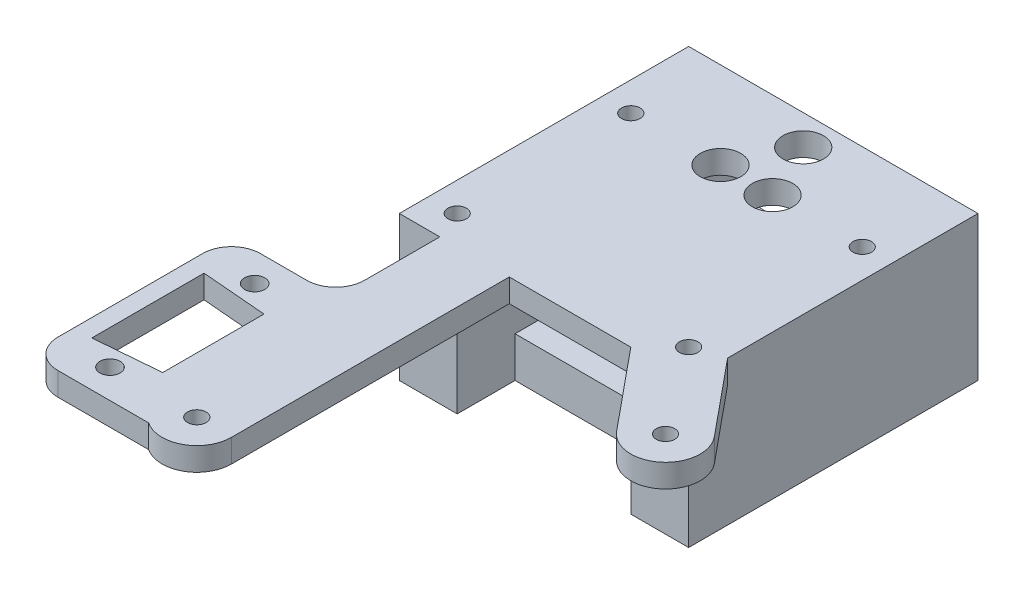
SolidWorks part; units mm, degrees
ref_plane "Plano frontal" through (0, 0, 0) normal (0, 0, 1) x (1, 0, 0)
ref_plane "Plano superior" through (0, 0, 0) normal (0, 1, 0) x (1, 0, 0)
ref_plane "Plano direito" through (0, 0, 0) normal (1, 0, 0) x (0, 0, -1)
sketch "Esboço1" plane through (0, 0, 0) normal (0, 0, 1) x (1, 0, 0)
  line L0 (-25, 0) -> (-15, 0)
  line L1 (-15, 0) -> (-15, -14)
  line L2 (-15, -14) -> (15, -14)
  line L3 (0, 3.4978) -> (0, -21) construction
  line L4 (25, -21) -> (-25, -21)
  line L5 (-25, -21) -> (-25, 0)
  line L6 (25, -21) -> (25, 0)
  line L7 (15, 0) -> (15, -14)
  line L8 (25, 0) -> (15, 0)
  point P9 (-20, 0)
  point P14 (0, -14)
  dimension "D1" = 40
  dimension "D2" = 10
  dimension "D3" = 14
  dimension "D4" = 7
extrude "Ressalto-extrusão1" add sketch "Esboço1" along normal blind 50
sketch "Esboço2" plane through (0, -21, 0) normal (0, -1, 0) x (1, 0, 0)
  line L0 (0, 0) -> (0, 50) construction
  line L1 (-25, 50) -> (25, 50) construction
  line L2 (-25, 0) -> (25, 0) construction
  line L3 (20, 45) -> (-20, 45) construction
  line L4 (20, 45) -> (20, 15) construction
  line L5 (20, 15) -> (-20, 15) construction
  line L6 (-20, 45) -> (-20, 15) construction
  line L7 (20, 45) -> (-20, 15) construction
  line L8 (20, 15) -> (-20, 45) construction
  line L9 (0, 16.6407) -> (0, 2.1283) construction
  circle A0 centre (-20, 45) radius 1.6
  circle A1 centre (20, 45) radius 1.6
  circle A2 centre (20, 15) radius 1.6
  circle A3 centre (-20, 15) radius 1.6
  circle A4 centre (-4.5, 15) radius 1.6
  circle A5 centre (0, 5.2) radius 1.6
  circle A6 centre (4.5, 15) radius 1.6
  point P5 (0, 30)
  dimension "D3" = 3.2
  dimension "D1" = 30
  dimension "D2" = 40
  dimension "D4" = 9
  dimension "D5" = 9.8
  dimension "D6" = 15
  dimension "D7" = 5
  dimension "D8" = 0
extrude "Corte-extrusão1" cut sketch "Esboço2" against normal blind 40
sketch "Esboço3" plane through (0, 0, 0) normal (0, 1, 0) x (1, 0, 0)
  line L0 (25, -43.2669) -> (35.6329, -56.1874)
  line L1 (26.3671, -63.8126) -> (15, -50)
  line L2 (-25, -50) -> (-18, -50)
  line L3 (-18, -50) -> (-18, -68)
  line L4 (-6, -98) -> (-6, -50)
  line L5 (-6, -50) -> (15, -50)
  line L6 (25, -43.2669) -> (25, 0)
  line L7 (25, 0) -> (-25, 0)
  line L8 (-25, 0) -> (-25, -50)
  line L9 (-25, -50) -> (-25, 0) construction
  line L10 (15, -50) -> (-15, -50) construction
  line L11 (25, -50) -> (25, 0) construction
  line L12 (25, -50) -> (15, -50) construction
  line L13 (-27, -98) -> (-27, -73) construction
  line L14 (-32.9409, -75.8) -> (-21.6409, -76.75)
  line L15 (-32.9409, -75.8) -> (-32.9409, -95.2)
  line L16 (-32.9409, -95.2) -> (-21.6409, -94.25)
  line L17 (-21.6409, -76.75) -> (-21.6409, -94.25)
  line L18 (-32.9409, -75.8) -> (-21.6409, -94.25) construction
  line L19 (-32.9409, -95.2) -> (-21.6409, -76.75) construction
  line L21 (-36, -68) -> (-18, -68)
  line L22 (-36, -68) -> (-36, -103)
  line L23 (-36, -103) -> (-15.3166, -103)
  line L25 (-36, -68) -> (-18, -103) construction
  line L26 (-36, -103) -> (-18, -68) construction
  arc A0 (35.6329, -56.1874) -> (26.3671, -63.8126) centre (31, -60) cw
  arc A1 (-15.3166, -103) -> (-6, -98) centre (-12, -98) ccw
  circle A2 centre (20, -45) radius 1.6 construction
  circle A3 centre (20, -15) radius 1.6 construction
  circle A4 centre (-20, -15) radius 1.6 construction
  circle A5 centre (-20, -45) radius 1.6 construction
  circle A6 centre (20, -45) radius 1.6
  circle A7 centre (20, -15) radius 1.6
  circle A8 centre (-20, -15) radius 1.6
  circle A9 centre (-20, -45) radius 1.6
  circle A10 centre (31, -60) radius 1.6
  circle A11 centre (-12, -98) radius 1.6
  circle A12 centre (-27, -98) radius 1.75
  circle A13 centre (-27, -73) radius 1.75
  circle A14 centre (0, -5.2) radius 3.5
  circle A15 centre (-4.5, -15) radius 3.5
  circle A16 centre (4.5, -15) radius 3.5
  point P43 (-27, -85.5)
  point P53 (-27, -85.5)
  point P54 (-21.6409, -85.5)
  point P55 (-32.9409, -85.5)
  dimension "D1" = 3.2
  dimension "D2" = 6
  dimension "D14" = 3.5
  dimension "D15" = 7
  dimension "D3" = 43
  dimension "D4" = 38
  dimension "D5" = 10
  dimension "D6" = 7
  dimension "D7" = 25
  dimension "D8" = 19.4
  dimension "D9" = 17.5
  dimension "D10" = 11.3
  dimension "D11" = 18
  dimension "D12" = 35
  dimension "D13" = 18
extrude "Ressalto-extrusão2" add sketch "Esboço3" along normal blind 4
sketch "Esboço4" plane through (0, -21, 0) normal (0, -1, 0) x (1, 0, 0)
  line L0 (-25, 50) -> (25, 50) construction
  line L1 (-15, 50) -> (15, 50)
  line L2 (-15, 50) -> (-15, 40)
  line L3 (-15, 40) -> (15, 40)
  line L4 (15, 50) -> (15, 40)
  line L5 (-15, 50) -> (-15, 0) construction
  line L6 (15, 50) -> (15, 0) construction
  dimension "D1" = 10
extrude "Corte-extrusão2" cut sketch "Esboço4" against normal up to surface (7 mm away) up to face at (6.1, -14, 15)
fillet "Filete1" radius 5 3 edges at (-36, 2, 103) (-36, 2, 68) (-18, 2, 68)
sketch "Esboço5" plane through (0, 4, 0) normal (0, 1, 0) x (1, 0, 0)
  circle A1 centre (4.5, -15) radius 3
  circle A2 centre (-4.5, -15) radius 3
  circle A3 centre (0, -5.2) radius 3
  dimension "D1" = 6
extrude "Corte-extrusão3" cut sketch "Esboço5" against normal blind 3 from surface at -18 starting at face at (6.1, -14, 15)
